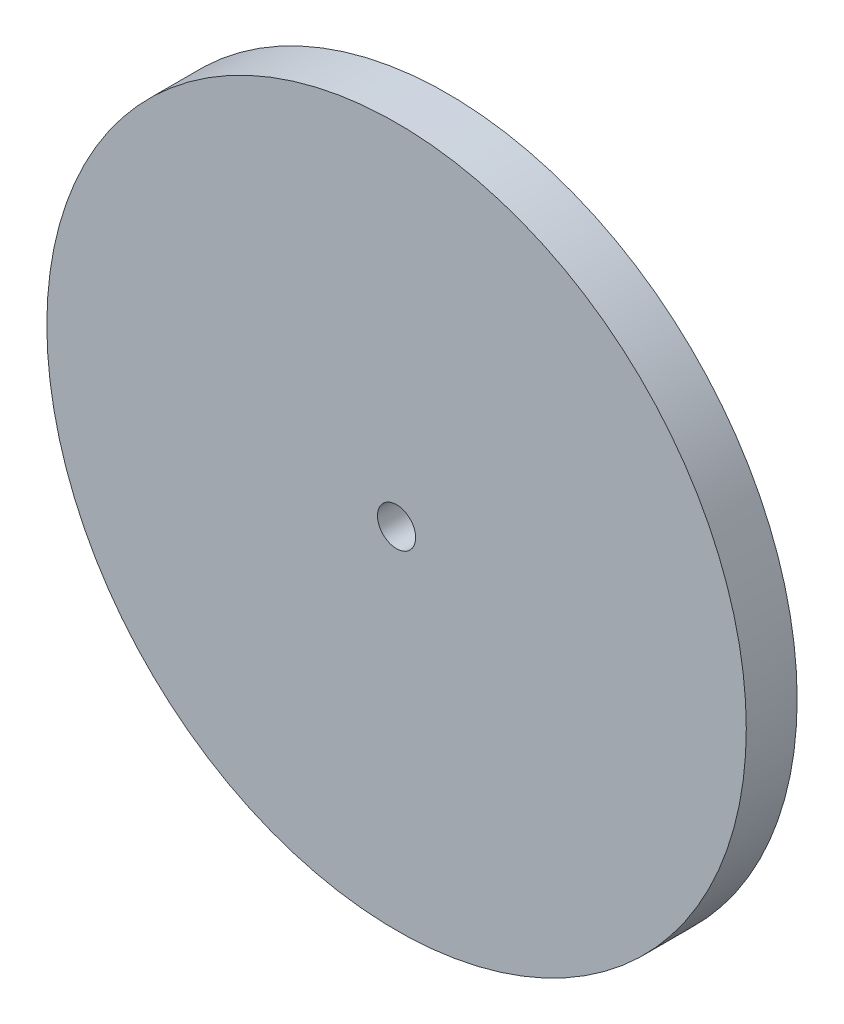
SolidWorks part; units mm, degrees
ref_plane "Front Plane" through (0, 0, 0) normal (0, 0, 1) x (1, 0, 0)
ref_plane "Top Plane" through (0, 0, 0) normal (0, 1, 0) x (1, 0, 0)
ref_plane "Right Plane" through (0, 0, 0) normal (1, 0, 0) x (0, 0, -1)
sketch "Sketch1" plane through (0, 0, 0) normal (0, 0, 1) x (1, 0, 0)
  circle A0 centre (0, 0) radius 17.4625
  circle A1 centre (0, 0) radius 0.9525
  dimension "D1" = 34.925
  dimension "D2" = 1.905
extrude "Boss-Extrude1" add sketch "Sketch1" along normal blind 2.54
